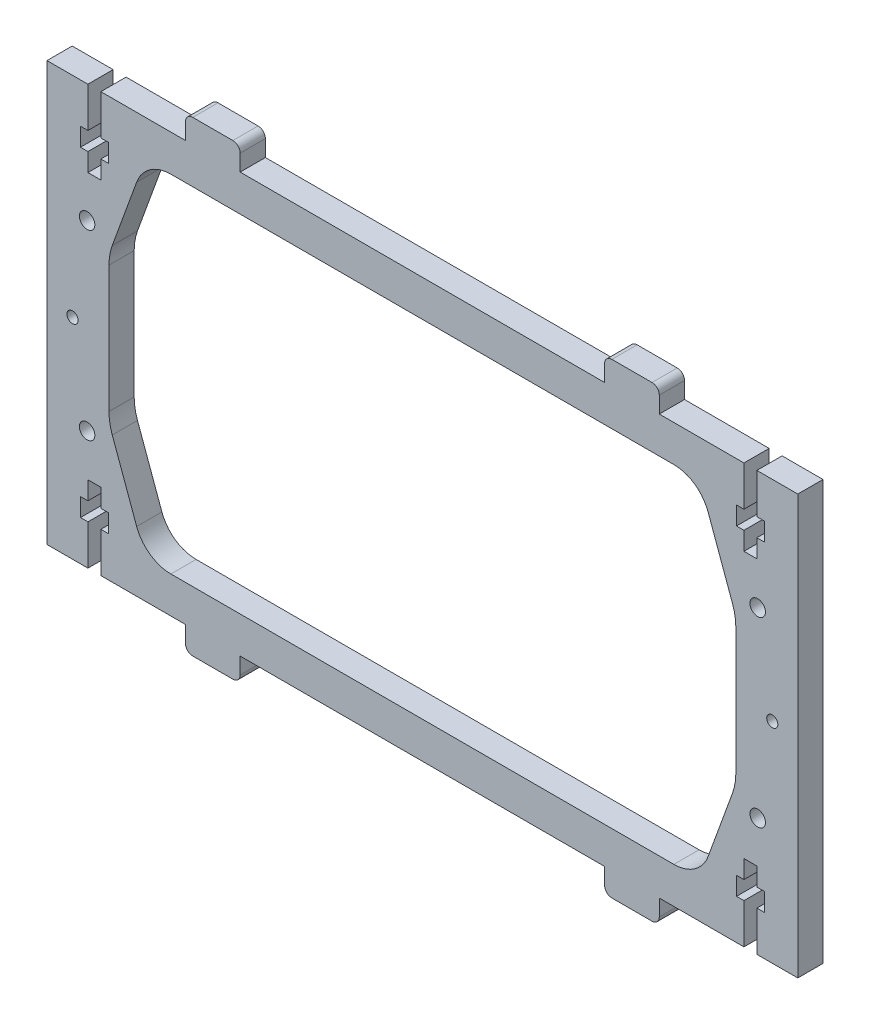
SolidWorks part; units mm, degrees
ref_plane "Front Plane" through (0, 0, 0) normal (0, 0, 1) x (1, 0, 0)
ref_plane "Top Plane" through (0, 0, 0) normal (0, 1, 0) x (1, 0, 0)
ref_plane "Right Plane" through (0, 0, 0) normal (1, 0, 0) x (0, 0, -1)
sketch "Sketch1" plane through (0, 0, 0) normal (0, 0, 1) x (1, 0, 0)
  line L0 (19.852, 81.0937) -> (19.852, 46.3217)
  line L1 (20.7566, 41.1914) -> (27.455, 22.7875)
  line L2 (36.852, 16.2077) -> (174.852, 16.2077)
  line L3 (184.2489, 22.7875) -> (190.9474, 41.1914)
  line L4 (191.852, 46.3217) -> (191.852, 81.0937)
  line L5 (190.9474, 86.224) -> (184.2489, 104.6279)
  line L6 (174.852, 111.2077) -> (36.852, 111.2077)
  line L7 (27.455, 104.6279) -> (20.7566, 86.224)
  line L8 (192.042, 105.2077) -> (192.042, 110.2077)
  line L9 (192.042, 110.2077) -> (194.077, 110.2077)
  line L10 (194.077, 110.2077) -> (194.077, 121.2077)
  line L11 (194.077, 121.2077) -> (170.852, 121.2077)
  line L12 (170.852, 121.2077) -> (170.852, 125.7077)
  line L13 (168.852, 127.7077) -> (157.852, 127.7077)
  line L14 (155.852, 125.7077) -> (155.852, 121.2077)
  line L15 (155.852, 121.2077) -> (55.852, 121.2077)
  line L16 (55.852, 121.2077) -> (55.852, 125.7077)
  line L17 (53.852, 127.7077) -> (42.852, 127.7077)
  line L18 (40.852, 125.7077) -> (40.852, 121.2077)
  line L19 (40.852, 121.2077) -> (17.627, 121.2077)
  line L20 (17.627, 121.2077) -> (17.627, 110.2077)
  line L21 (17.627, 110.2077) -> (19.662, 110.2077)
  line L22 (19.662, 110.2077) -> (19.662, 105.2077)
  line L23 (19.662, 105.2077) -> (17.627, 105.2077)
  line L24 (17.627, 105.2077) -> (17.627, 100.2077)
  line L25 (17.627, 100.2077) -> (14.077, 100.2077)
  line L26 (14.077, 100.2077) -> (14.077, 105.2077)
  line L27 (14.077, 105.2077) -> (12.042, 105.2077)
  line L28 (12.042, 105.2077) -> (12.042, 110.2077)
  line L29 (12.042, 110.2077) -> (14.077, 110.2077)
  line L30 (14.077, 110.2077) -> (14.077, 121.2077)
  line L31 (14.077, 121.2077) -> (2.852, 121.2077)
  line L32 (2.852, 121.2077) -> (2.852, 6.2077)
  line L33 (2.852, 6.2077) -> (14.077, 6.2077)
  line L34 (14.077, 6.2077) -> (14.077, 17.2077)
  line L35 (14.077, 17.2077) -> (12.042, 17.2077)
  line L36 (12.042, 17.2077) -> (12.042, 22.2077)
  line L37 (12.042, 22.2077) -> (14.077, 22.2077)
  line L38 (14.077, 22.2077) -> (14.077, 27.2077)
  line L39 (14.077, 27.2077) -> (17.627, 27.2077)
  line L40 (17.627, 27.2077) -> (17.627, 22.2077)
  line L41 (17.627, 22.2077) -> (19.662, 22.2077)
  line L42 (19.662, 22.2077) -> (19.662, 17.2077)
  line L43 (19.662, 17.2077) -> (17.627, 17.2077)
  line L44 (17.627, 17.2077) -> (17.627, 6.2077)
  line L45 (17.627, 6.2077) -> (40.852, 6.2077)
  line L46 (40.852, 6.2077) -> (40.852, 1.7077)
  line L47 (42.852, -0.2923) -> (53.852, -0.2923)
  line L48 (55.852, 1.7077) -> (55.852, 6.2077)
  line L49 (55.852, 6.2077) -> (155.852, 6.2077)
  line L50 (155.852, 6.2077) -> (155.852, 1.7077)
  line L51 (157.852, -0.2923) -> (168.852, -0.2923)
  line L52 (170.852, 1.7077) -> (170.852, 6.2077)
  line L53 (170.852, 6.2077) -> (194.077, 6.2077)
  line L54 (194.077, 6.2077) -> (194.077, 17.2077)
  line L55 (194.077, 17.2077) -> (192.042, 17.2077)
  line L56 (192.042, 17.2077) -> (192.042, 22.2077)
  line L57 (192.042, 22.2077) -> (194.077, 22.2077)
  line L58 (194.077, 22.2077) -> (194.077, 27.2077)
  line L59 (194.077, 27.2077) -> (197.627, 27.2077)
  line L60 (197.627, 27.2077) -> (197.627, 22.2077)
  line L61 (197.627, 22.2077) -> (199.662, 22.2077)
  line L62 (199.662, 22.2077) -> (199.662, 17.2077)
  line L63 (199.662, 17.2077) -> (197.627, 17.2077)
  line L64 (197.627, 17.2077) -> (197.627, 6.2077)
  line L65 (197.627, 6.2077) -> (208.852, 6.2077)
  line L66 (208.852, 6.2077) -> (208.852, 121.2077)
  line L67 (208.852, 121.2077) -> (197.627, 121.2077)
  line L68 (197.627, 121.2077) -> (197.627, 110.2077)
  line L69 (197.627, 110.2077) -> (199.662, 110.2077)
  line L70 (199.662, 110.2077) -> (199.662, 105.2077)
  line L71 (199.662, 105.2077) -> (197.627, 105.2077)
  line L72 (197.627, 105.2077) -> (197.627, 100.2077)
  line L73 (197.627, 100.2077) -> (194.077, 100.2077)
  line L74 (194.077, 100.2077) -> (194.077, 105.2077)
  line L75 (194.077, 105.2077) -> (192.042, 105.2077)
  circle A0 centre (13.852, 38.7077) radius 2.125
  circle A1 centre (197.852, 88.7077) radius 2.125
  circle A2 centre (13.852, 88.7077) radius 2.125
  circle A3 centre (197.852, 38.7077) radius 2.125
  circle A4 centre (9.852, 63.7077) radius 1.524
  circle A5 centre (201.852, 63.7077) radius 1.524
  arc A6 (19.852, 46.3217) -> (20.7566, 41.1914) centre (34.852, 46.3217) ccw
  arc A7 (27.455, 22.7875) -> (36.852, 16.2077) centre (36.852, 26.2077) ccw
  arc A8 (174.852, 16.2077) -> (184.2489, 22.7875) centre (174.852, 26.2077) ccw
  arc A9 (190.9474, 41.1914) -> (191.852, 46.3217) centre (176.852, 46.3217) ccw
  arc A10 (191.852, 81.0937) -> (190.9474, 86.224) centre (176.852, 81.0937) ccw
  arc A11 (184.2489, 104.6279) -> (174.852, 111.2077) centre (174.852, 101.2077) ccw
  arc A12 (36.852, 111.2077) -> (27.455, 104.6279) centre (36.852, 101.2077) ccw
  arc A13 (20.7566, 86.224) -> (19.852, 81.0937) centre (34.852, 81.0937) ccw
  arc A14 (170.852, 125.7077) -> (168.852, 127.7077) centre (168.852, 125.7077) ccw
  arc A15 (157.852, 127.7077) -> (155.852, 125.7077) centre (157.852, 125.7077) ccw
  arc A16 (55.852, 125.7077) -> (53.852, 127.7077) centre (53.852, 125.7077) ccw
  arc A17 (42.852, 127.7077) -> (40.852, 125.7077) centre (42.852, 125.7077) ccw
  arc A18 (40.852, 1.7077) -> (42.852, -0.2923) centre (42.852, 1.7077) ccw
  arc A19 (53.852, -0.2923) -> (55.852, 1.7077) centre (53.852, 1.7077) ccw
  arc A20 (155.852, 1.7077) -> (157.852, -0.2923) centre (157.852, 1.7077) ccw
  arc A21 (168.852, -0.2923) -> (170.852, 1.7077) centre (168.852, 1.7077) ccw
extrude "Boss-Extrude1" add sketch "Sketch1" along normal blind 6.92
